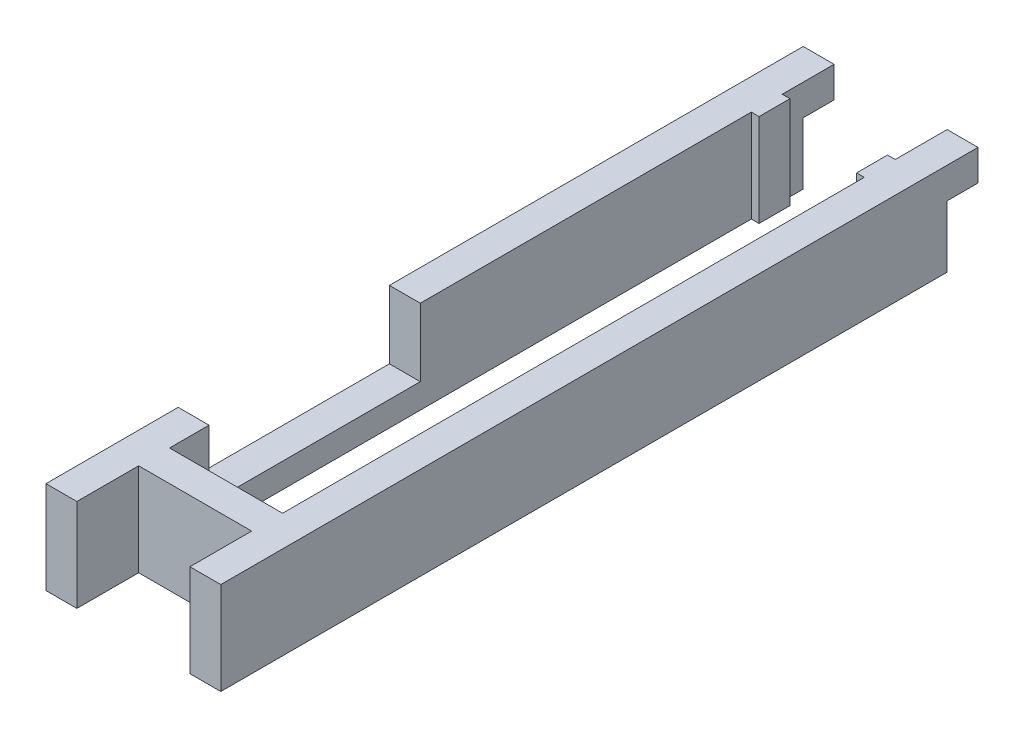
SolidWorks part; units mm, degrees
ref_plane "Front" through (0, 0, 0) normal (0, 0, 1) x (1, 0, 0)
ref_plane "Bottom" through (0, 0, 0) normal (0, 1, 0) x (1, 0, 0)
ref_plane "Right" through (0, 0, 0) normal (1, 0, 0) x (0, 0, -1)
sketch "Sketch1" plane through (0, 0, 0) normal (0, 1, 0) x (1, 0, 0)
  line L0 (-10.033, 66.167) -> (-11.6205, 66.167)
  line L2 (-11.6205, -66.167) -> (11.6205, -66.167)
  line L4 (11.6205, 66.167) -> (10.033, 66.167)
  line L5 (10.033, 66.167) -> (10.033, 59.817)
  line L6 (10.033, 59.817) -> (11.6205, 59.817)
  line L7 (11.6205, 59.817) -> (11.6205, -59.817)
  line L8 (11.6205, -59.817) -> (-11.6205, -59.817)
  line L9 (-11.6205, -59.817) -> (-11.6205, 59.817)
  line L10 (-11.6205, 59.817) -> (-10.033, 59.817)
  line L11 (-10.033, 59.817) -> (-10.033, 66.167)
  line L12 (-17.9705, -78.867) -> (-17.9705, 76.835)
  line L13 (-17.9705, 76.835) -> (-11.6205, 76.835)
  line L14 (-11.6205, 76.835) -> (-11.6205, 66.167)
  line L15 (11.6205, 66.167) -> (11.6205, 76.835)
  line L16 (11.6205, 76.835) -> (17.9705, 76.835)
  line L17 (17.9705, 76.835) -> (17.9705, -78.867)
  line L21 (-17.9705, -78.867) -> (-11.6205, -78.867)
  line L22 (-11.6205, -66.167) -> (-11.6205, -78.867)
  line L25 (17.9705, -78.867) -> (11.6205, -78.867)
  line L26 (11.6205, -66.167) -> (11.6205, -78.867)
  point P2 (-17.9705, -77.0507)
  point P12 (0, -59.817)
  point P13 (-11.6205, 0)
  point P22 (-8.2781, -93.6592)
  point P23 (17.9705, -108.0894)
  point P24 (0, 0)
  point P25 (-10.8267, 59.817)
  point P26 (17.9705, -44.6507)
  point P27 (17.9705, -76.5062)
  dimension "D1" = 6.35
  dimension "D2" = 6.35
  dimension "D3" = 6.35
  dimension "D4" = 1.5875
  dimension "D5" = 17.018
  dimension "D6" = 23.241
  dimension "D7" = 119.634
  dimension "D8" = 12.7
extrude "Boss-Extrude1" add sketch "Sketch1" along normal blind 19.05
sketch "Sketch2" plane through (-17.9705, 0, 0) normal (-1, 0, 0) x (0, 0, 1)
  line L0 (-76.835, 19.05) -> (78.867, 19.05) construction
  line L1 (8.255, 19.05) -> (51.689, 19.05)
  line L2 (8.255, 19.05) -> (8.255, 5.08)
  line L3 (8.255, 5.08) -> (51.689, 5.08)
  line L4 (51.689, 19.05) -> (51.689, 5.08)
  line L6 (-76.835, 0) -> (78.867, 0) construction
  dimension "D1" = 8.128
  dimension "D2" = 51.562
  dimension "D3" = 5.08
extrude "Motor Hole" cut sketch "Sketch2" against normal blind 19.05
sketch "Sketch3" plane through (-17.9705, 0, 0) normal (-1, 0, 0) x (0, 0, 1)
  line L0 (-76.835, 19.05) -> (-76.835, 0) construction
  line L1 (-76.835, 0) -> (-70.485, 0)
  line L2 (-76.835, 0) -> (-76.835, 12.7)
  line L3 (-76.835, 12.7) -> (-70.485, 12.7)
  line L4 (-70.485, 0) -> (-70.485, 12.7)
  line L6 (-76.835, 0) -> (78.867, 0) construction
  point P6 (-70.485, 6.6027)
  point P12 (0, 0)
  point P15 (-70.485, 9.3319)
  dimension "D1" = 12.7
  dimension "D2" = 6.35
extrude "Cut-Extrude2" cut sketch "Sketch3" against normal through all
sketch "Sketch5" plane through (-17.9705, 0, 0) normal (-1, 0, 0) x (0, 0, 1)
  line L0 (51.689, 19.05) -> (78.867, 19.05) construction
  line L1 (59.817, 19.05) -> (66.167, 19.05)
  line L2 (59.817, 19.05) -> (59.817, 5.08)
  line L3 (59.817, 5.08) -> (66.167, 5.08)
  line L4 (66.167, 19.05) -> (66.167, 5.08)
  line L5 (8.255, 5.08) -> (51.689, 5.08) construction
  line L6 (78.867, 19.05) -> (78.867, 0) construction
  line L7 (-66.167, 12.7) -> (-59.817, 12.7)
  line L8 (-66.167, 12.7) -> (-66.167, 6.35)
  line L9 (-66.167, 6.35) -> (-59.817, 6.35)
  line L10 (-59.817, 12.7) -> (-59.817, 6.35)
  point P8 (0, 0)
  point P10 (0, 0)
  point P18 (-66.167, 9.525)
  point P21 (78.867, 9.525)
  dimension "D1" = 6.35
extrude "Cut-Extrude6" [suppressed] cut sketch "Sketch5" against normal through all
sketch "Sketch7" plane through (0, 0, 0) normal (0, 1, 0) x (1, 0, 0)
  line L1 (11.6205, -78.867) -> (-34.3558, -78.867)
  line L2 (11.6205, -78.867) -> (11.6205, 80.9204)
  line L3 (11.6205, 80.9204) -> (-34.3558, 80.9204)
  line L4 (-34.3558, -78.867) -> (-34.3558, 80.9204)
  point P5 (-34.3558, -78.867)
  point P6 (0, 0)
  point P7 (11.6205, -78.867)
  point P9 (0, 0)
extrude "Cut-Extrude7" [suppressed] cut sketch "Sketch7" along normal through all
